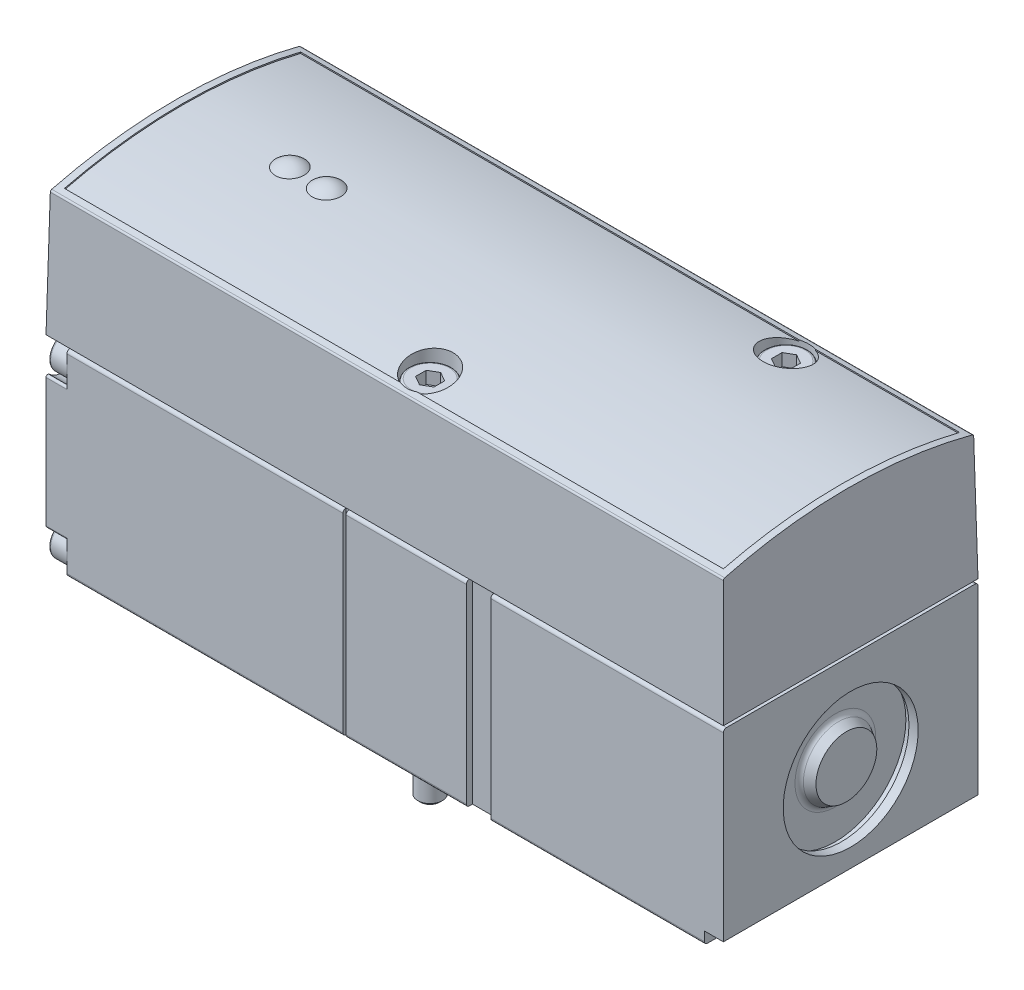
SolidWorks part; units mm, degrees
ref_plane "Front Plane" through (0, 0, 0) normal (0, 0, 1) x (1, 0, 0)
ref_plane "Top Plane" through (0, 0, 0) normal (0, 1, 0) x (1, 0, 0)
ref_plane "Right Plane" through (0, 0, 0) normal (1, 0, 0) x (0, 0, -1)
ref_plane "Plane1" through (0, 0, 0) normal (1, 0, 0) x (0, 0, -1)
sketch "Sketch1" plane through (0, 0, 0) normal (1, 0, 0) x (0, 0, -1)
  line L0 (-20.75, 31.5) -> (-20.75, 0.5)
  line L1 (-20.25, 0) -> (20.25, 0)
  line L2 (20.75, 0.5) -> (20.75, 31.5)
  line L3 (20.25, 32) -> (-20.25, 32)
  arc A0 (-20.75, 0.5) -> (-20.25, 0) centre (-20.25, 0.5) ccw
  arc A1 (20.25, 0) -> (20.75, 0.5) centre (20.25, 0.5) ccw
  arc A2 (20.75, 31.5) -> (20.25, 32) centre (20.25, 31.5) ccw
  arc A3 (-20.25, 32) -> (-20.75, 31.5) centre (-20.25, 31.5) ccw
extrude "Boss-Extrude1" add sketch "Sketch1" against normal blind 110.4
ref_plane "Plane2" through (-61.5, 0, 0) normal (1, 0, 0) x (0, 0, -1)
sketch "Sketch2" plane through (-61.5, 0, 0) normal (1, 0, 0) x (0, 0, -1)
  line L0 (-25, 39) -> (-25, -1)
  line L1 (-25, -1) -> (25, -1)
  line L2 (25, -1) -> (25, 39)
  line L3 (25, 39) -> (-25, 39)
  line L4 (-20.25, 32.5) -> (-20.25, 0.5)
  line L5 (-20.25, 0.5) -> (20.25, 0.5)
  line L6 (20.25, 0.5) -> (20.25, 32.5)
  line L7 (20.25, 32.5) -> (-20.25, 32.5)
extrude "Cut-Extrude1" cut sketch "Sketch2" against normal blind 0.5
ref_plane "Plane3" through (-0.9, 0, 0) normal (1, 0, 0) x (0, 0, -1)
sketch "Sketch3" plane through (-0.9, 0, 0) normal (1, 0, 0) x (0, 0, -1)
  line L0 (-19.85, 31.5) -> (19.85, 31.5)
  line L1 (19.85, 31.5) -> (19.85, 33.5)
  line L2 (19.85, 33.5) -> (-19.85, 33.5)
  line L3 (-19.85, 33.5) -> (-19.85, 31.5)
extrude "Boss-Extrude2" add sketch "Sketch3" against normal blind 108.6
ref_plane "Plane4" through (0, 0, 0) normal (1, 0, 0) x (0, 0, -1)
sketch "Sketch4" plane through (0, 0, 0) normal (1, 0, 0) x (0, 0, -1)
  line L0 (-20.75, 32.5) -> (20.75, 32.5)
  line L1 (20.75, 32.5) -> (20.3985, 52.6361)
  line L2 (-20.3985, 52.6361) -> (-20.75, 32.5)
  arc A0 (20.3985, 52.6361) -> (20.174, 52.9212) centre (20.0986, 52.6308) ccw
  arc A1 (20.174, 52.9212) -> (-20.174, 52.9212) centre (0, -24.7) ccw
  arc A2 (-20.174, 52.9212) -> (-20.3985, 52.6361) centre (-20.0986, 52.6308) ccw
extrude "Boss-Extrude3" add sketch "Sketch4" against normal blind 110.4
ref_plane "Plane5" through (0, 56, 0) normal (0, 1, 0) x (1, 0, 0)
sketch "Sketch5" plane through (0, 56, 0) normal (0, 1, 0) x (1, 0, 0)
  line L0 (-108.9, -19.25) -> (-1.5, -19.25)
  line L1 (-1.5, -19.25) -> (-1.5, 19.25)
  line L2 (-1.5, 19.25) -> (-108.9, 19.25)
  line L3 (-108.9, 19.25) -> (-108.9, -19.25)
extrude "Cut-Extrude2" cut sketch "Sketch5" against normal blind 10
ref_plane "Plane6" through (0, 0, 0) normal (1, 0, 0) x (0, 0, -1)
sketch "Sketch6" plane through (0, 0, 0) normal (1, 0, 0) x (0, 0, -1)
  line L0 (-20.75, 32.5) -> (20.75, 32.5)
  line L1 (20.75, 32.5) -> (20.4021, 52.4285)
  line L2 (-20.4021, 52.4285) -> (-20.75, 32.5)
  arc A0 (20.4021, 52.4285) -> (20.1779, 52.7135) centre (20.1022, 52.4232) ccw
  arc A1 (20.1779, 52.7135) -> (-20.1779, 52.7135) centre (0, -24.7) ccw
  arc A2 (-20.1779, 52.7135) -> (-20.4021, 52.4285) centre (-20.1022, 52.4232) ccw
extrude "Boss-Extrude4" add sketch "Sketch6" against normal blind 110.4
ref_plane "Plane7" through (0, 0, 0) normal (0, 0, 1) x (1, 0, 0)
sketch "Sketch7" plane through (0, 0, 0) normal (0, 0, 1) x (1, 0, 0)
  line L0 (-111.4, 32.5) -> (-110.4, 32.5)
  line L1 (-110.4, 32.5) -> (-109.7891, 67.5)
  line L2 (-109.7891, 67.5) -> (-0.6109, 67.5)
  line L3 (-0.6109, 67.5) -> (0, 32.5)
  line L4 (0, 32.5) -> (1, 32.5)
  line L5 (1, 32.5) -> (1, 70)
  line L6 (1, 70) -> (-111.4, 70)
  line L7 (-111.4, 70) -> (-111.4, 32.5)
extrude "Cut-Extrude3" cut sketch "Sketch7" against normal blind 22 and the other way blind 22
ref_plane "Plane8" through (-110.4, 0, 0) normal (1, 0, 0) x (0, 0, -1)
sketch "Sketch8" plane through (-110.4, 0, 0) normal (1, 0, 0) x (0, 0, -1)
  line L0 (-23, 32) -> (-23, -1)
  line L1 (-23, -1) -> (23, -1)
  line L2 (23, -1) -> (23, 32)
  line L3 (23, 32) -> (15.2224, 32)
  line L4 (20.75, 26.4724) -> (20.75, 5.5276)
  line L5 (15.2224, 0) -> (-15.2224, 0)
  line L6 (-20.75, 5.5276) -> (-20.75, 26.4724)
  line L7 (-15.2224, 32) -> (-23, 32)
  arc A0 (15.2224, 32) -> (15.4435, 31.4973) centre (15.2224, 31.7) cw
  arc A1 (15.4435, 31.4973) -> (20.2473, 26.6935) centre (17.95, 29.2) ccw
  arc A2 (20.2473, 26.6935) -> (20.75, 26.4724) centre (20.45, 26.4724) cw
  arc A3 (20.75, 5.5276) -> (20.2473, 5.3065) centre (20.45, 5.5276) cw
  arc A4 (20.2473, 5.3065) -> (15.4435, 0.5027) centre (17.95, 2.8) ccw
  arc A5 (15.4435, 0.5027) -> (15.2224, 0) centre (15.2224, 0.3) cw
  arc A6 (-15.2224, 0) -> (-15.4435, 0.5027) centre (-15.2224, 0.3) cw
  arc A7 (-15.4435, 0.5027) -> (-20.2473, 5.3065) centre (-17.95, 2.8) ccw
  arc A8 (-20.2473, 5.3065) -> (-20.75, 5.5276) centre (-20.45, 5.5276) cw
  arc A9 (-20.75, 26.4724) -> (-20.2473, 26.6935) centre (-20.45, 26.4724) cw
  arc A10 (-20.2473, 26.6935) -> (-15.4435, 31.4973) centre (-17.95, 29.2) ccw
  arc A11 (-15.4435, 31.4973) -> (-15.2224, 32) centre (-15.2224, 31.7) cw
extrude "Cut-Extrude4" cut sketch "Sketch8" along normal blind 3.4
ref_plane "Plane9" through (0, 0, -17.95) normal (0, 0, 1) x (1, 0, 0)
sketch "Sketch9" plane through (0, 0, -17.95) normal (0, 0, 1) x (1, 0, 0)
  line L0 (-110, 2.8) -> (-110, 5.25)
  line L1 (-109.7, 5.55) -> (-107, 5.55)
  line L2 (-107, 5.55) -> (-107, 2.8)
  line L3 (-107, 2.8) -> (-110, 2.8)
  line L4 (-107, 2.8) -> (-110, 2.8) construction
  arc A0 (-110, 5.25) -> (-109.7, 5.55) centre (-109.7, 5.25) cw
revolve "Revolve1" add sketch "Sketch9" angle 360 about L4
ref_plane "Plane10" through (0, 0, -17.95) normal (0, 0, 1) x (1, 0, 0)
sketch "Sketch10" plane through (0, 0, -17.95) normal (0, 0, 1) x (1, 0, 0)
  line L0 (-110, 29.2) -> (-110, 31.65)
  line L1 (-109.7, 31.95) -> (-107, 31.95)
  line L2 (-107, 31.95) -> (-107, 29.2)
  line L3 (-107, 29.2) -> (-110, 29.2)
  line L4 (-107, 29.2) -> (-110, 29.2) construction
  arc A0 (-110, 31.65) -> (-109.7, 31.95) centre (-109.7, 31.65) cw
revolve "Revolve2" add sketch "Sketch10" angle 360 about L4
ref_plane "Plane11" through (0, 0, 17.95) normal (0, 0, 1) x (1, 0, 0)
sketch "Sketch11" plane through (0, 0, 17.95) normal (0, 0, 1) x (1, 0, 0)
  line L0 (-110, 2.8) -> (-110, 5.25)
  line L1 (-109.7, 5.55) -> (-107, 5.55)
  line L2 (-107, 5.55) -> (-107, 2.8)
  line L3 (-107, 2.8) -> (-110, 2.8)
  line L4 (-107, 2.8) -> (-110, 2.8) construction
  arc A0 (-110, 5.25) -> (-109.7, 5.55) centre (-109.7, 5.25) cw
revolve "Revolve3" add sketch "Sketch11" angle 360 about L4
ref_plane "Plane12" through (0, 0, 17.95) normal (0, 0, 1) x (1, 0, 0)
sketch "Sketch12" plane through (0, 0, 17.95) normal (0, 0, 1) x (1, 0, 0)
  line L0 (-110, 29.2) -> (-110, 31.65)
  line L1 (-109.7, 31.95) -> (-107, 31.95)
  line L2 (-107, 31.95) -> (-107, 29.2)
  line L3 (-107, 29.2) -> (-110, 29.2)
  line L4 (-107, 29.2) -> (-110, 29.2) construction
  arc A0 (-110, 31.65) -> (-109.7, 31.95) centre (-109.7, 31.65) cw
revolve "Revolve4" add sketch "Sketch12" angle 360 about L4
ref_plane "Plane13" through (-110, 0, 0) normal (1, 0, 0) x (0, 0, -1)
sketch "Sketch13" plane through (-110, 0, 0) normal (1, 0, 0) x (0, 0, -1)
  line L0 (16.7, 3.5217) -> (16.7, 2.0783)
  line L1 (16.7, 2.0783) -> (17.95, 1.3566)
  line L2 (17.95, 1.3566) -> (19.2, 2.0783)
  line L3 (19.2, 2.0783) -> (19.2, 3.5217)
  line L4 (19.2, 3.5217) -> (17.95, 4.2434)
  line L5 (17.95, 4.2434) -> (16.7, 3.5217)
extrude "Cut-Extrude5" cut sketch "Sketch13" along normal blind 1.3
ref_plane "Plane14" through (-110, 0, 0) normal (1, 0, 0) x (0, 0, -1)
sketch "Sketch14" plane through (-110, 0, 0) normal (1, 0, 0) x (0, 0, -1)
  line L0 (-19.2, 3.5217) -> (-19.2, 2.0783)
  line L1 (-19.2, 2.0783) -> (-17.95, 1.3566)
  line L2 (-17.95, 1.3566) -> (-16.7, 2.0783)
  line L3 (-16.7, 2.0783) -> (-16.7, 3.5217)
  line L4 (-16.7, 3.5217) -> (-17.95, 4.2434)
  line L5 (-17.95, 4.2434) -> (-19.2, 3.5217)
extrude "Cut-Extrude6" cut sketch "Sketch14" along normal blind 1.3
ref_plane "Plane15" through (-110, 0, 0) normal (1, 0, 0) x (0, 0, -1)
sketch "Sketch15" plane through (-110, 0, 0) normal (1, 0, 0) x (0, 0, -1)
  line L0 (16.7, 29.9217) -> (16.7, 28.4783)
  line L1 (16.7, 28.4783) -> (17.95, 27.7566)
  line L2 (17.95, 27.7566) -> (19.2, 28.4783)
  line L3 (19.2, 28.4783) -> (19.2, 29.9217)
  line L4 (19.2, 29.9217) -> (17.95, 30.6434)
  line L5 (17.95, 30.6434) -> (16.7, 29.9217)
extrude "Cut-Extrude7" cut sketch "Sketch15" along normal blind 1.3
ref_plane "Plane16" through (-110, 0, 0) normal (1, 0, 0) x (0, 0, -1)
sketch "Sketch16" plane through (-110, 0, 0) normal (1, 0, 0) x (0, 0, -1)
  line L0 (-19.2, 29.9217) -> (-19.2, 28.4783)
  line L1 (-19.2, 28.4783) -> (-17.95, 27.7566)
  line L2 (-17.95, 27.7566) -> (-16.7, 28.4783)
  line L3 (-16.7, 28.4783) -> (-16.7, 29.9217)
  line L4 (-16.7, 29.9217) -> (-17.95, 30.6434)
  line L5 (-17.95, 30.6434) -> (-19.2, 29.9217)
extrude "Cut-Extrude8" cut sketch "Sketch16" along normal blind 1.3
ref_plane "Plane17" through (-52.8, 0, 0) normal (1, 0, 0) x (0, 0, -1)
sketch "Sketch17" plane through (-52.8, 0, 0) normal (1, 0, 0) x (0, 0, -1)
  line L0 (-15.75, -11.4) -> (-17.95, -11.4)
  line L1 (-17.95, -11.4) -> (-17.95, 48.6)
  line L2 (-17.95, 48.6) -> (-19.5, 48.6)
  line L3 (-19.5, 48.6) -> (-19.5, 56.6)
  line L4 (-19.5, 56.6) -> (-15.75, 56.6)
  line L5 (-15.75, 56.6) -> (-15.75, -11.4)
  line L6 (-15.75, 56.6) -> (-15.75, -11.4) construction
revolve "Cut-Revolve1" cut sketch "Sketch17" angle 360 about L6
ref_plane "Plane18" through (-26.3, 0, 0) normal (1, 0, 0) x (0, 0, -1)
sketch "Sketch18" plane through (-26.3, 0, 0) normal (1, 0, 0) x (0, 0, -1)
  line L0 (15.75, -11.4) -> (13.55, -11.4)
  line L1 (13.55, -11.4) -> (13.55, 48.6)
  line L2 (13.55, 48.6) -> (12, 48.6)
  line L3 (12, 48.6) -> (12, 56.6)
  line L4 (12, 56.6) -> (15.75, 56.6)
  line L5 (15.75, 56.6) -> (15.75, -11.4)
  line L6 (15.75, 56.6) -> (15.75, -11.4) construction
revolve "Cut-Revolve2" cut sketch "Sketch18" angle 360 about L6
ref_plane "Plane19" through (-52.8, 0, 0) normal (1, 0, 0) x (0, 0, -1)
sketch "Sketch19" plane through (-52.8, 0, 0) normal (1, 0, 0) x (0, 0, -1)
  line L0 (-15.75, -6.4) -> (-17.3205, -6.4)
  line L1 (-17.3205, -6.4) -> (-17.75, -5.9705)
  line L2 (-17.75, -5.9705) -> (-17.75, 48.6)
  line L3 (-17.75, 48.6) -> (-19.25, 48.6)
  line L4 (-19.25, 48.6) -> (-19.25, 52.2)
  line L5 (-18.85, 52.6) -> (-15.75, 52.6)
  line L6 (-15.75, 52.6) -> (-15.75, -6.4)
  line L7 (-15.75, 52.6) -> (-15.75, -6.4) construction
  arc A0 (-19.25, 52.2) -> (-18.85, 52.6) centre (-18.85, 52.2) cw
revolve "Revolve5" add sketch "Sketch19" angle 360 about L7
cosmetic thread "Cosmetic Thread1" parameters "D1"=20, "D2"=3.141
ref_plane "Plane20" through (-26.3, 0, 0) normal (1, 0, 0) x (0, 0, -1)
sketch "Sketch20" plane through (-26.3, 0, 0) normal (1, 0, 0) x (0, 0, -1)
  line L0 (15.75, -6.4) -> (14.1795, -6.4)
  line L1 (14.1795, -6.4) -> (13.75, -5.9705)
  line L2 (13.75, -5.9705) -> (13.75, 48.6)
  line L3 (13.75, 48.6) -> (12.25, 48.6)
  line L4 (12.25, 48.6) -> (12.25, 52.2)
  line L5 (12.65, 52.6) -> (15.75, 52.6)
  line L6 (15.75, 52.6) -> (15.75, -6.4)
  line L7 (15.75, 52.6) -> (15.75, -6.4) construction
  arc A0 (12.25, 52.2) -> (12.65, 52.6) centre (12.65, 52.2) cw
revolve "Revolve6" add sketch "Sketch20" angle 360 about L7
cosmetic thread "Cosmetic Thread2" parameters "D1"=20, "D2"=3.141
ref_plane "Plane21" through (0, 52.6, 0) normal (0, 1, 0) x (1, 0, 0)
sketch "Sketch21" plane through (0, 52.6, 0) normal (0, 1, 0) x (1, 0, 0)
  line L0 (-54.3, -16.616) -> (-52.8, -17.4821)
  line L1 (-52.8, -17.4821) -> (-51.3, -16.616)
  line L2 (-51.3, -16.616) -> (-51.3, -14.884)
  line L3 (-51.3, -14.884) -> (-52.8, -14.0179)
  line L4 (-52.8, -14.0179) -> (-54.3, -14.884)
  line L5 (-54.3, -14.884) -> (-54.3, -16.616)
extrude "Cut-Extrude9" cut sketch "Sketch21" against normal blind 2
ref_plane "Plane22" through (0, 52.6, 0) normal (0, 1, 0) x (1, 0, 0)
sketch "Sketch22" plane through (0, 52.6, 0) normal (0, 1, 0) x (1, 0, 0)
  line L0 (-27.8, 14.884) -> (-26.3, 14.0179)
  line L1 (-26.3, 14.0179) -> (-24.8, 14.884)
  line L2 (-24.8, 14.884) -> (-24.8, 16.616)
  line L3 (-24.8, 16.616) -> (-26.3, 17.4821)
  line L4 (-26.3, 17.4821) -> (-27.8, 16.616)
  line L5 (-27.8, 16.616) -> (-27.8, 14.884)
extrude "Cut-Extrude10" cut sketch "Sketch22" against normal blind 2
ref_plane "Plane23" through (0, 0, 0) normal (0, 0, 1) x (1, 0, 0)
sketch "Sketch23" plane through (0, 0, 0) normal (0, 0, 1) x (1, 0, 0)
  line L0 (-0.7, 16) -> (-0.7, 20.9608)
  line L1 (-0.7, 20.9608) -> (-2, 21.7113)
  line L2 (-2.5, 22.5774) -> (-2.5, 27.5)
  line L3 (-2.5, 27.5) -> (-1.5, 27.5)
  line L4 (-1.5, 27.5) -> (-1.5, 27)
  line L5 (-1.5, 27) -> (0, 27)
  line L6 (0, 27) -> (0, 16)
  line L7 (0, 16) -> (-0.7, 16)
  line L8 (0, 16) -> (-2.5, 16) construction
  arc A0 (-2, 21.7113) -> (-2.5, 22.5774) centre (-1.5, 22.5774) cw
revolve "Cut-Revolve3" cut sketch "Sketch23" angle 360 about L8
ref_plane "Plane24" through (0, 0, 0) normal (0, 1, 0) x (1, 0, 0)
sketch "Sketch24" plane through (0, 0, 0) normal (0, 1, 0) x (1, 0, 0)
  circle A0 centre (-12.2, -7.6) radius 3
extrude "Cut-Extrude11" cut sketch "Sketch24" along normal blind 16
ref_plane "Plane25" through (0, 0, 0) normal (0, 1, 0) x (1, 0, 0)
sketch "Sketch25" plane through (0, 0, 0) normal (0, 1, 0) x (1, 0, 0)
  line L0 (-21.9213, -2.1213) -> (-14.3213, -9.7213)
  line L1 (-10.0787, -5.4787) -> (-17.6787, 2.1213)
  arc A0 (-17.6787, 2.1213) -> (-21.9213, -2.1213) centre (-19.8, 0) ccw
  arc A1 (-14.3213, -9.7213) -> (-10.0787, -5.4787) centre (-12.2, -7.6) ccw
extrude "Cut-Extrude12" cut sketch "Sketch25" along normal blind 5.5
ref_plane "Plane26" through (0, 0, 0) normal (0, 1, 0) x (1, 0, 0)
sketch "Sketch26" plane through (0, 0, 0) normal (0, 1, 0) x (1, 0, 0)
  line L0 (-41.3, 1.25) -> (-39.3, 1.25)
  line L1 (-39.3, 1.25) -> (-39.3, -1.6947)
  line L2 (-36.8, -15.75) -> (-28.3, -15.75)
  line L3 (-23.1735, -13.6265) -> (-19.8, -10.253)
  line L4 (-19.8, -10.253) -> (-17.3265, -12.7265)
  line L5 (-7.0735, -2.4735) -> (-14.6749, 5.1279)
  line L6 (-27.05, 0.1438) -> (-27.05, -1.25)
  line L7 (-27.05, -1.25) -> (-36.8, -1.25)
  line L8 (-36.8, -1.25) -> (-36.8, 1.6947)
  line L9 (-39.3, 15.75) -> (-41.3, 15.75)
  line L10 (-24.55, -0.1138) -> (-24.55, -1.9675)
  line L11 (-24.55, -1.9675) -> (-15.5588, -10.9588)
  line L12 (-8.8412, -4.2412) -> (-16.4426, 3.3602)
  line L13 (-36.8, -13.25) -> (-28.3, -13.25)
  line L14 (-24.9412, -11.8588) -> (-21.5662, -8.4838)
  line L15 (-21.5662, -8.4838) -> (-26.3, -3.75)
  line L16 (-26.3, -3.75) -> (-36.8, -3.75)
  line L17 (-41.3, 3.75) -> (-39.3, 3.75)
  line L18 (-39.3, 13.25) -> (-41.3, 13.25)
  arc A0 (-41.3, 15.75) -> (-41.3, 1.25) centre (-41.3, 8.5) ccw
  arc A1 (-39.3, -1.6947) -> (-36.8, -15.75) centre (-36.8, -8.5) ccw
  arc A2 (-28.3, -15.75) -> (-23.1735, -13.6265) centre (-28.3, -8.5) ccw
  arc A3 (-17.3265, -12.7265) -> (-7.0735, -2.4735) centre (-12.2, -7.6) ccw
  arc A4 (-14.6749, 5.1279) -> (-27.05, 0.1438) centre (-19.8014, 0.0014) ccw
  arc A5 (-36.8, 1.6947) -> (-39.3, 15.75) centre (-39.3, 8.5) ccw
  arc A6 (-16.4426, 3.3602) -> (-24.55, -0.1138) centre (-19.8014, 0.0014) ccw
  arc A7 (-15.5588, -10.9588) -> (-8.8412, -4.2412) centre (-12.2, -7.6) ccw
  arc A8 (-36.8, -3.75) -> (-36.8, -13.25) centre (-36.8, -8.5) ccw
  arc A9 (-28.3, -13.25) -> (-24.9412, -11.8588) centre (-28.3, -8.5) ccw
  arc A10 (-41.3, 13.25) -> (-41.3, 3.75) centre (-41.3, 8.5) ccw
  arc A11 (-39.3, 3.75) -> (-39.3, 13.25) centre (-39.3, 8.5) ccw
extrude "Cut-Extrude13" cut sketch "Sketch26" along normal blind 0.4
ref_plane "Plane27" through (0, 0, 0) normal (0, 1, 0) x (1, 0, 0)
sketch "Sketch27" plane through (0, 0, 0) normal (0, 1, 0) x (1, 0, 0)
  circle A0 centre (-41.3, 8.5) radius 3
extrude "Cut-Extrude14" cut sketch "Sketch27" along normal blind 16
ref_plane "Plane28" through (0, 0, 0) normal (0, 1, 0) x (1, 0, 0)
sketch "Sketch28" plane through (0, 0, 0) normal (0, 1, 0) x (1, 0, 0)
  circle A0 centre (-28.3, -8.5) radius 3
extrude "Cut-Extrude15" cut sketch "Sketch28" along normal blind 16
ref_plane "Plane29" through (0, 0, 0) normal (0, 1, 0) x (1, 0, 0)
sketch "Sketch29" plane through (0, 0, 0) normal (0, 1, 0) x (1, 0, 0)
  line L0 (-36.8, -11.5) -> (-28.3, -11.5)
  line L1 (-28.3, -5.5) -> (-36.8, -5.5)
  arc A0 (-36.8, -5.5) -> (-36.8, -11.5) centre (-36.8, -8.5) ccw
  arc A1 (-28.3, -11.5) -> (-28.3, -5.5) centre (-28.3, -8.5) ccw
extrude "Cut-Extrude16" cut sketch "Sketch29" along normal blind 5.5
ref_plane "Plane30" through (0, 0, 0) normal (1, 0, 0) x (0, 0, -1)
sketch "Sketch30" plane through (0, 0, 0) normal (1, 0, 0) x (0, 0, -1)
  line L0 (-20.75, 2) -> (-20.75, 0)
  line L1 (-20.75, 0) -> (20.75, 0)
  line L2 (20.75, 0) -> (20.75, 2)
  line L3 (20.75, 2) -> (-20.75, 2)
extrude "Cut-Extrude17" cut sketch "Sketch30" against normal blind 3.1
ref_plane "Plane31" through (-37.9, 0, 0) normal (1, 0, 0) x (0, 0, -1)
sketch "Sketch31" plane through (-37.9, 0, 0) normal (1, 0, 0) x (0, 0, -1)
  line L0 (-22, 32) -> (-22, -1)
  line L1 (-22, -1) -> (0, -1)
  line L2 (0, -1) -> (0, 0)
  line L3 (0, 0) -> (-19.75, 0)
  line L4 (-19.75, 0) -> (-19.75, 32)
  line L5 (-19.75, 32) -> (-22, 32)
extrude "Cut-Extrude18" cut sketch "Sketch31" against normal blind 4
ref_plane "Plane32" through (-34.1, 0, 0) normal (1, 0, 0) x (0, 0, -1)
sketch "Sketch32" plane through (-34.1, 0, 0) normal (1, 0, 0) x (0, 0, -1)
  line L0 (0, -1) -> (22, -1)
  line L1 (22, -1) -> (22, 32)
  line L2 (22, 32) -> (19.75, 32)
  line L3 (19.75, 32) -> (19.75, 0)
  line L4 (19.75, 0) -> (0, 0)
  line L5 (0, 0) -> (0, -1)
extrude "Cut-Extrude19" cut sketch "Sketch32" against normal blind 4
ref_plane "Plane33" through (0, 0, 0) normal (0, 0, 1) x (1, 0, 0)
sketch "Sketch33" plane through (0, 0, 0) normal (0, 0, 1) x (1, 0, 0)
  line L0 (-81.94, 52.74) -> (-94.86, 52.74)
  line L1 (-81.94, 52.74) -> (-94.86, 52.74) construction
  arc A0 (-94.86, 52.74) -> (-88.4, 54.4638) centre (-91.4, 52.74) cw
  arc A1 (-88.4, 54.4638) -> (-81.94, 52.74) centre (-85.4, 52.74) cw
revolve "Revolve7" add sketch "Sketch33" angle 360 about L1
ref_plane "Plane34" through (0, 0, 0) normal (0, 1, 0) x (1, 0, 0)
sketch "Sketch34" plane through (0, 0, 0) normal (0, 1, 0) x (1, 0, 0)
  line L0 (-98.32, 7) -> (-92.58, 7)
  line L1 (-92.58, 14.8) -> (-98.32, 14.8)
  arc A0 (-98.32, 14.8) -> (-98.32, 7) centre (-98.32, 10.9) ccw
  arc A1 (-92.58, 7) -> (-92.58, 14.8) centre (-92.58, 10.9) ccw
extrude "Cut-Extrude20" cut sketch "Sketch34" along normal blind 6.2
ref_plane "Plane35" through (-91.2, 0, 0) normal (1, 0, 0) x (0, 0, -1)
sketch "Sketch35" plane through (-91.2, 0, 0) normal (1, 0, 0) x (0, 0, -1)
  line L0 (9.625, 2.4192) -> (9.7774, 1.962)
  line L1 (9.7774, 1.962) -> (9.9726, 1.962)
  line L2 (9.9726, 1.962) -> (10.125, 2.4192)
  line L3 (10.125, 2.4192) -> (10.125, 6.762)
  line L4 (10.125, 6.762) -> (11.625, 6.762)
  line L5 (11.625, 6.762) -> (11.625, 2.4192)
  line L6 (11.625, 2.4192) -> (11.7774, 1.962)
  line L7 (11.7774, 1.962) -> (11.9726, 1.962)
  line L8 (11.9726, 1.962) -> (12.125, 2.4192)
  line L9 (12.125, 2.4192) -> (12.125, 6.962)
  line L10 (12.125, 6.962) -> (9.625, 6.962)
  line L11 (9.625, 6.962) -> (9.625, 2.4192)
extrude "Boss-Extrude5" add sketch "Sketch35" against normal blind 8.5
ref_plane "Plane36" through (0, 0, -9.625) normal (0, 0, 1) x (1, 0, 0)
sketch "Sketch36" plane through (0, 0, -9.625) normal (0, 0, 1) x (1, 0, 0)
  line L0 (-100, 1.2) -> (-91, 1.2)
  line L1 (-91, 1.2) -> (-91, 6.2)
  line L2 (-91, 6.2) -> (-91.2, 6.2)
  line L3 (-91.2, 6.2) -> (-91.2, 2.4192)
  line L4 (-91.2, 2.4192) -> (-91.3524, 1.962)
  line L5 (-91.3524, 1.962) -> (-91.5476, 1.962)
  line L6 (-91.5476, 1.962) -> (-91.7, 2.4192)
  line L7 (-91.7, 2.4192) -> (-91.7, 6.2)
  line L8 (-91.7, 6.2) -> (-93.2, 6.2)
  line L9 (-93.2, 6.2) -> (-93.2, 2.4192)
  line L10 (-93.2, 2.4192) -> (-93.3524, 1.962)
  line L11 (-93.3524, 1.962) -> (-93.5476, 1.962)
  line L12 (-93.5476, 1.962) -> (-93.7, 2.4192)
  line L13 (-93.7, 2.4192) -> (-93.7, 6.2)
  line L14 (-93.7, 6.2) -> (-95.2, 6.2)
  line L15 (-95.2, 6.2) -> (-95.2, 2.4192)
  line L16 (-95.2, 2.4192) -> (-95.3524, 1.962)
  line L17 (-95.3524, 1.962) -> (-95.5476, 1.962)
  line L18 (-95.5476, 1.962) -> (-95.7, 2.4192)
  line L19 (-95.7, 2.4192) -> (-95.7, 6.2)
  line L20 (-95.7, 6.2) -> (-97.2, 6.2)
  line L21 (-97.2, 6.2) -> (-97.2, 2.4192)
  line L22 (-97.2, 2.4192) -> (-97.3524, 1.962)
  line L23 (-97.3524, 1.962) -> (-97.5476, 1.962)
  line L24 (-97.5476, 1.962) -> (-97.7, 2.4192)
  line L25 (-97.7, 2.4192) -> (-97.7, 6.2)
  line L26 (-97.7, 6.2) -> (-99.2, 6.2)
  line L27 (-99.2, 6.2) -> (-99.2, 2.4192)
  line L28 (-99.2, 2.4192) -> (-99.3524, 1.962)
  line L29 (-99.3524, 1.962) -> (-99.5476, 1.962)
  line L30 (-99.5476, 1.962) -> (-99.7, 2.4192)
  line L31 (-99.7, 2.4192) -> (-99.7, 6.2)
  line L32 (-99.7, 6.2) -> (-100, 6.2)
  line L33 (-100, 6.2) -> (-100, 1.2)
extrude "Cut-Extrude21" cut sketch "Sketch36" against normal blind 3
